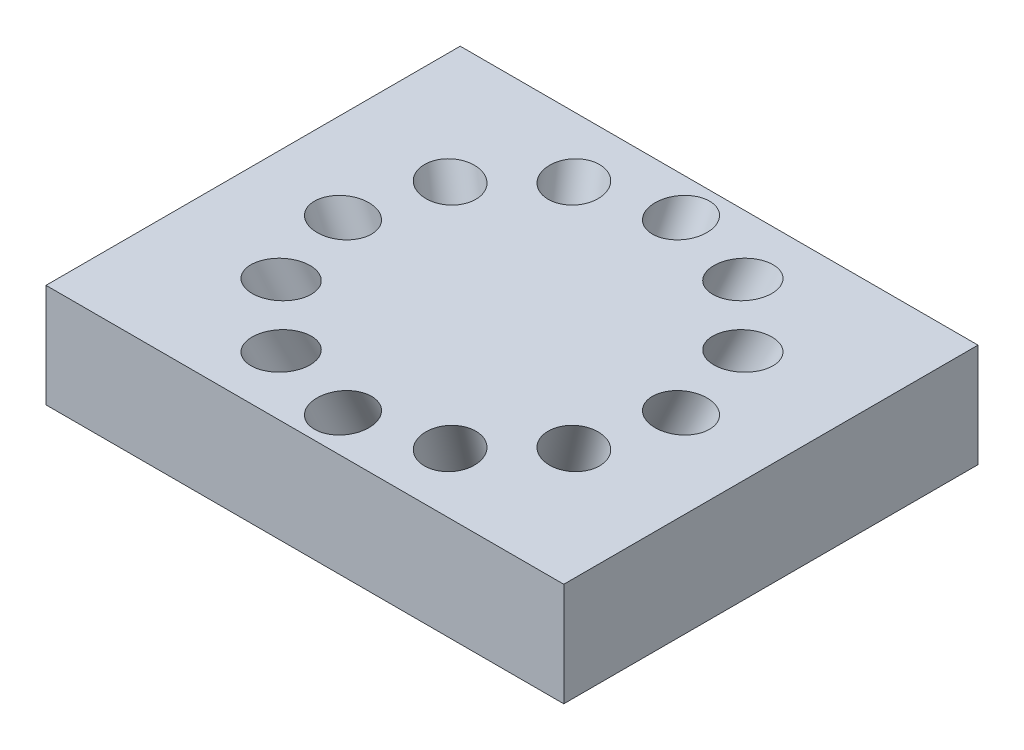
SolidWorks part; units mm, degrees
ref_plane "Vorne" through (0, 0, 0) normal (0, 0, 1) x (1, 0, 0)
ref_plane "Oben" through (0, 0, 0) normal (0, 1, 0) x (1, 0, 0)
ref_plane "Rechts" through (0, 0, 0) normal (1, 0, 0) x (0, 0, -1)
sketch "Skizze1" plane through (0, 0, 0) normal (0, 1, 0) x (1, 0, 0)
  line L1 (-50, 40) -> (50, 40)
  line L2 (-50, 40) -> (-50, -40)
  line L3 (-50, -40) -> (50, -40)
  line L4 (50, 40) -> (50, -40)
  line L5 (-50, 40) -> (50, -40) construction
  line L6 (-50, -40) -> (50, 40) construction
  point P0 (0, 0)
  dimension "D1" = 100
  dimension "D2" = 80
extrude "Aufsatz-Linear austragen1" add sketch "Skizze1" along normal blind 20
sketch "Skizze2" plane through (0, 0, 0) normal (0, 0, 1) x (1, 0, 0)
  line L0 (0, 0) -> (0, -50) construction
  line L1 (0, -50) -> (-41.6265, 39.2682) construction
  line L3 (-33.6269, 22.1131) -> (-22.33, -2.1131)
  line L4 (-33.6269, 22.1131) -> (-29.0953, 24.2262)
  line L5 (-22.33, -2.1131) -> (-17.7985, 0)
  line L6 (-29.0953, 24.2262) -> (-17.7985, 0)
  line L9 (-33.6269, 22.1131) -> (-38.1584, 20) construction
  line L10 (-50, 20) -> (50, 20) construction
  line L11 (-50, 0) -> (50, 0) construction
  dimension "D1" = 25
  dimension "D2" = 50
  dimension "D3" = 10
revolve "Schnitt-Rotation1" cut sketch "Skizze2" angle 360 about L1
pattern_circular "Kreismuster1" count 12 over 360 of "Schnitt-Rotation1"
